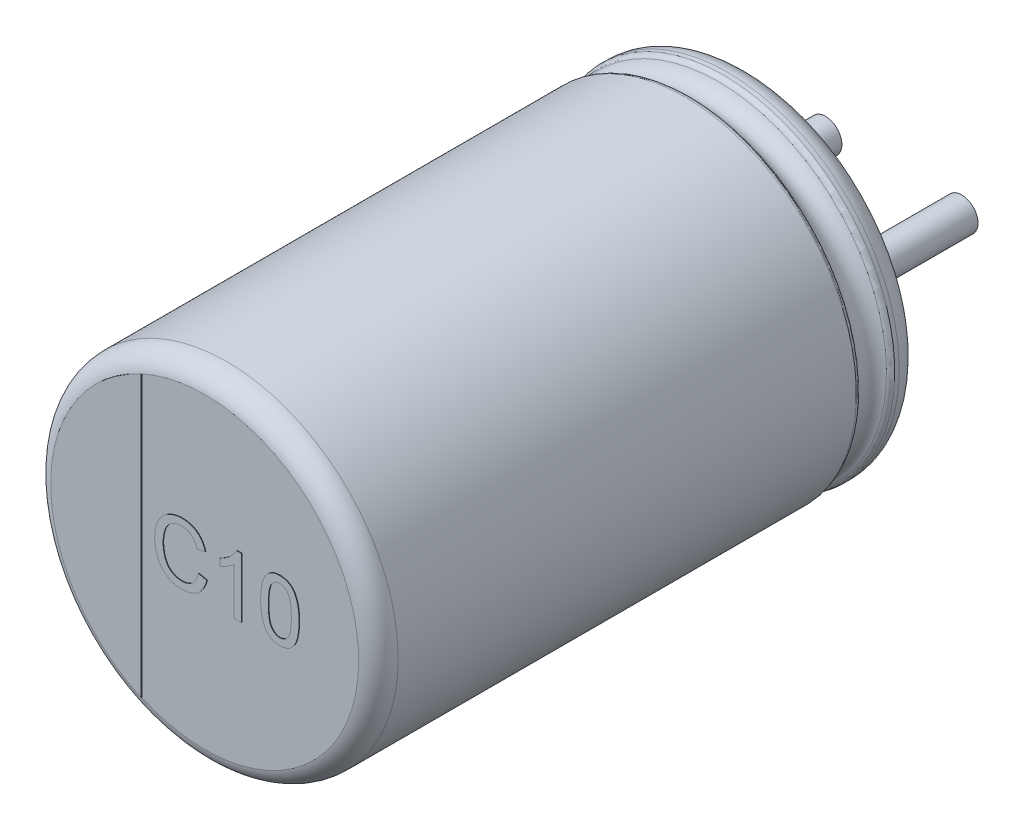
SolidWorks part; units mm, degrees
ref_plane "Plan de face" through (0, 0, 0) normal (0, 0, 1) x (1, 0, 0)
ref_plane "Plan de dessus" through (0, 0, 0) normal (0, 1, 0) x (1, 0, 0)
ref_plane "Plan de droite" through (0, 0, 0) normal (1, 0, 0) x (0, 0, -1)
sketch "Sketch10" plane through (0, 0, 0) normal (1, 0, 0) x (0, 0, -1)
  line L0 (18.1631, 0) -> (-18.9631, 0) construction
  line L1 (-10, 0) -> (-0.05, 0)
  line L2 (-10, 0) -> (-10, 2.8236)
  line L3 (-9.6, 3.15) -> (-1.1846, 3.15)
  line L4 (-0.05, 2.5531) -> (-0.05, 0)
  line L7 (-0.4794, 3.15) -> (-0.3982, 3.15)
  arc A0 (-10, 2.8236) -> (-9.6, 3.15) centre (-9.6068, 2.7501) cw
  arc A1 (-0.3982, 3.15) -> (-0.05, 2.5531) centre (-0.3982, 2.75) cw
  arc A2 (-0.5713, 3.0894) -> (-1.0926, 3.0894) centre (-0.832, 3.201) cw
  arc A3 (-1.0926, 3.0894) -> (-1.1846, 3.15) centre (-1.1846, 3.05) ccw
  arc A4 (-0.5713, 3.0894) -> (-0.4794, 3.15) centre (-0.4794, 3.05) cw
  point P4 (0.57, 0)
  point P13 (-10, 3.15)
  dimension "D2" = 0.4
  dimension "D3" = 0.4
  dimension "D4" = 0.1
  dimension "D5" = 0.1
  dimension "D1" = 3.15
  dimension "D7" = 0.05
  dimension "D8" = 3.15
revolve "Повернуть1" add sketch "Sketch10" angle 360 about L0
sketch "Эскиз2" plane through (0, 0, 0.05) normal (0, 0, -1) x (-1, 0, 0)
  line L1 (0, 0.7993) -> (0, -1.0496) construction
  line L2 (-1.25, 0) -> (3.6313, 0) construction
  circle A3 centre (-1.25, 0) radius 0.3
  circle A7 centre (1.25, 0) radius 0.3
  dimension "D1" = 2.5
extrude "Бобышка-Вытянуть1" add sketch "Эскиз2" along normal blind 2.7
sketch "Эскиз4" plane through (0, 0, 10) normal (0, 0, 1) x (1, 0, 0)
  line L0 (-1.1603, -2.5741) -> (-1.1603, 2.5741)
  circle A1 centre (0, 0) radius 2.8236 construction
  arc A2 (-1.1603, 2.5741) -> (-1.1603, -2.5741) centre (0, 0) ccw
extrude "Бобышка-Вытянуть2" add sketch "Эскиз4" along normal blind 0.01
sketch "Эскиз5" plane through (0, 0, 10) normal (0, 0, 1) x (1, 0, 0)
  text T0 "C10" font "Arial" height 1.1
extrude "Текст" add sketch "Эскиз5" along normal blind 0.01
sketch "Эскиз6" plane through (0, 0, 0.05) normal (0, 0, -1) x (-1, 0, 0)
  line L0 (-1.25, 0.4) -> (-1.6248, 0.4)
  line L1 (-1.25, -0.4) -> (-1.6248, -0.4)
  line L2 (1.25, -0.4) -> (1.6248, -0.4)
  line L3 (1.25, 0.4) -> (1.6248, 0.4)
  arc A0 (-1.8569, -0.7429) -> (1.8569, -0.7429) centre (0, 0) ccw
  arc A1 (-1.25, -0.4) -> (-1.25, 0.4) centre (-1.25, 0) ccw
  arc A2 (1.25, 0.4) -> (1.25, -0.4) centre (1.25, 0) ccw
  arc A3 (1.8569, 0.7429) -> (-1.8569, 0.7429) centre (0, 0) ccw
  arc A4 (1.6248, 0.4) -> (1.8569, 0.7429) centre (1.6248, 0.65) ccw
  arc A5 (1.6248, -0.4) -> (1.8569, -0.7429) centre (1.6248, -0.65) cw
  arc A6 (-1.8569, -0.7429) -> (-1.6248, -0.4) centre (-1.6248, -0.65) cw
  arc A7 (-1.6248, 0.4) -> (-1.8569, 0.7429) centre (-1.6248, 0.65) cw
  point P7 (1.9596, 0.4)
  point P23 (0, -2)
  point P24 (0, 2)
  dimension "D1" = 0.25
  dimension "D2" = 4
extrude "Бобышка-Вытянуть5" add sketch "Эскиз6" along normal blind 0.05 contours A3 A7 L0 A1 L1 A6 A0 A5 L2 A2 L3 A4
